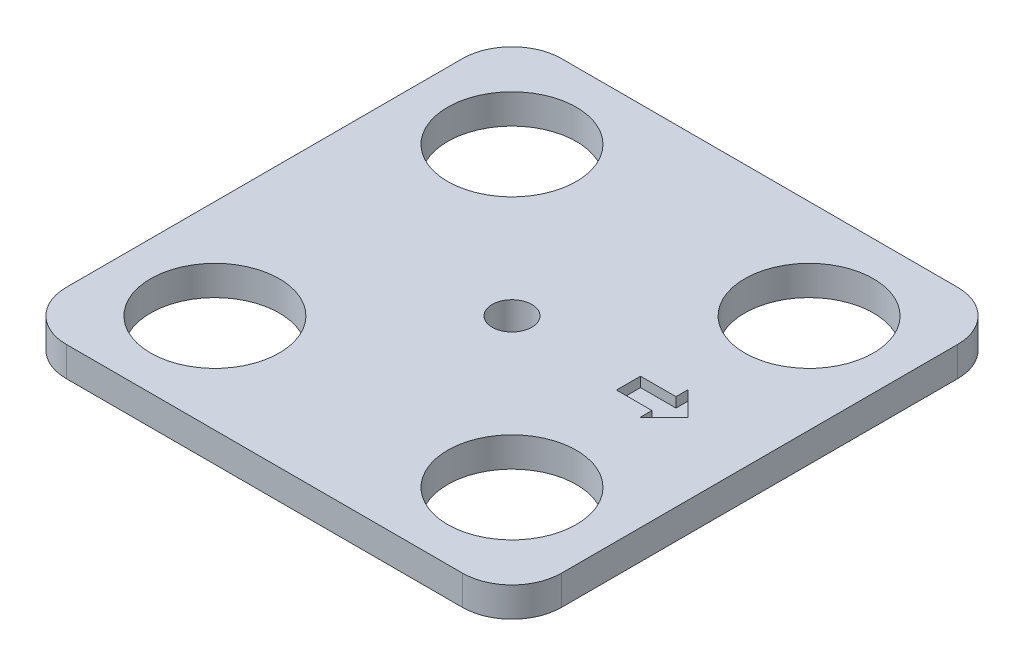
SolidWorks part; units mm, degrees
ref_plane "前视基准面" through (0, 0, 0) normal (0, 0, 1) x (1, 0, 0)
ref_plane "上视基准面" through (0, 0, 0) normal (0, 1, 0) x (1, 0, 0)
ref_plane "右视基准面" through (0, 0, 0) normal (1, 0, 0) x (0, 0, -1)
sketch "草图1" plane through (0, 0, 0) normal (0, 1, 0) x (1, 0, 0)
  line L1 (250, -250) -> (-250, -250)
  line L2 (250, -250) -> (250, 250)
  line L3 (250, 250) -> (-250, 250)
  line L4 (-250, -250) -> (-250, 250)
  line L5 (250, -250) -> (-250, 250) construction
  line L6 (250, 250) -> (-250, -250) construction
  point P0 (0, 0)
  dimension "D1" = 500
  dimension "D2" = 500
extrude "凸台-拉伸1" add sketch "草图1" along normal blind 30
sketch "草图2" plane through (0, 30, 0) normal (0, 1, 0) x (1, 0, 0)
  line L1 (-150, 150) -> (150, 150) construction
  line L2 (-150, 150) -> (-150, -150) construction
  line L3 (-150, -150) -> (150, -150) construction
  line L4 (150, 150) -> (150, -150) construction
  line L5 (-150, 150) -> (150, -150) construction
  line L6 (-150, -150) -> (150, 150) construction
  circle A0 centre (150, -150) radius 65
  circle A1 centre (-150, -150) radius 65
  circle A2 centre (150, 150) radius 65
  circle A3 centre (-150, 150) radius 65
  point P0 (0, 0)
  dimension "D3" = 130
  dimension "D4" = 130
  dimension "D5" = 130
  dimension "D6" = 130
  dimension "D1" = 300
  dimension "D2" = 300
extrude "切除-拉伸1" cut sketch "草图2" against normal blind 30
fillet "圆角1" radius 50 4 edges at (250, 15, -250) (-250, 15, -250) (-250, 15, 250) (250, 15, 250)
sketch "草图3" plane through (0, 30, 0) normal (0, 1, 0) x (1, 0, 0)
  line L0 (250, 0) -> (-250, 0) construction
  line L1 (250, -200) -> (250, 200) construction
  line L2 (-250, 200) -> (-250, -200) construction
  line L3 (177.7204, 0) -> (153.4553, 24.2651)
  line L4 (153.4553, 24.2651) -> (153.4553, 12.1325)
  line L5 (153.4553, 12.1325) -> (117.6438, 12.1325)
  line L6 (117.6438, 12.1325) -> (117.6438, -12.1325)
  line L7 (153.4553, -12.1325) -> (117.6438, -12.1325)
  line L8 (153.4553, -24.2651) -> (153.4553, -12.1325)
  line L9 (177.7204, 0) -> (153.4553, -24.2651)
  point P12 (117.6438, 0)
extrude "切除-拉伸2" cut sketch "草图3" against normal blind 10
sketch "草图4" plane through (0, 30, 0) normal (0, 1, 0) x (1, 0, 0)
  line L0 (0, 250) -> (0, -250) construction
  line L1 (200, 250) -> (-200, 250) construction
  line L2 (-200, -250) -> (200, -250) construction
  circle A0 centre (0, 0) radius 20
extrude "切除-拉伸3" cut sketch "草图4" against normal through all
